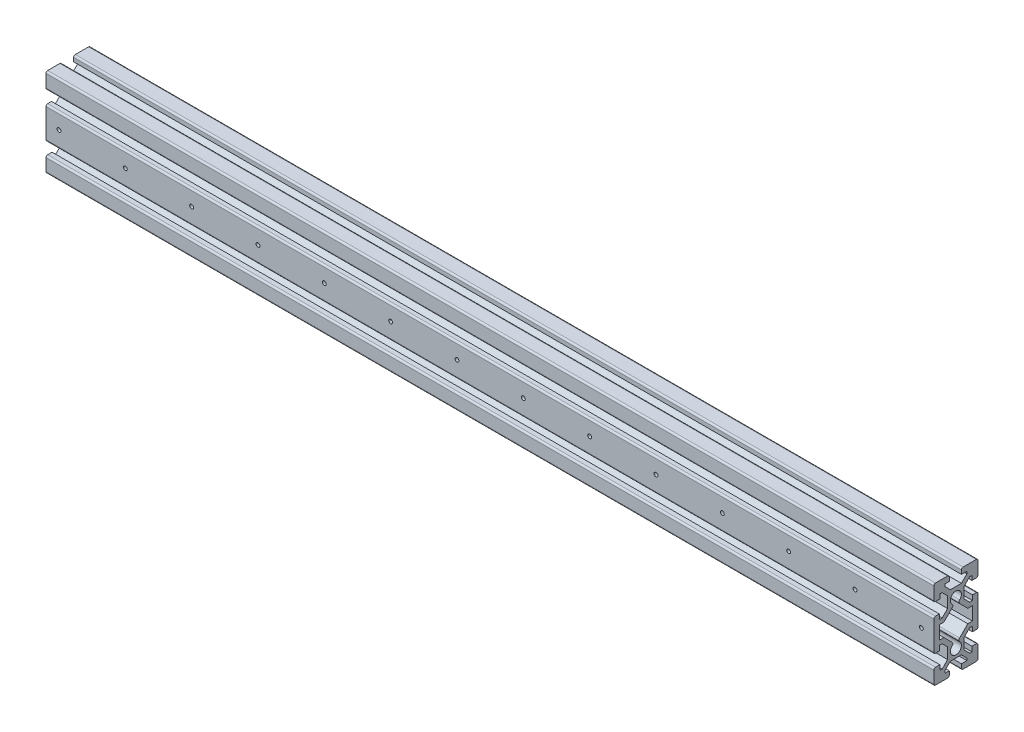
SolidWorks part; units mm, degrees
ref_plane "Piano frontale" through (0, 0, 0) normal (0, 0, 1) x (1, 0, 0)
ref_plane "Piano superiore" through (0, 0, 0) normal (0, 1, 0) x (1, 0, 0)
ref_plane "Piano destro" through (0, 0, 0) normal (1, 0, 0) x (0, 0, -1)
sketch "Schizzo1" plane through (0, 0, 0) normal (1, 0, 0) x (0, 0, -1)
  line L0 (20, 40.5) -> (5, 40.5) construction
  line L1 (18.5, -39.5) -> (6.5, -39.5)
  line L2 (-15, 6.0503) -> (-10.7929, 6.0503)
  line L3 (18.5, 40.5) -> (6.5, 40.5)
  line L4 (-20, -38) -> (-20, -27)
  line L7 (20, -39.5) -> (5, -39.5) construction
  line L21 (-12.4497, 10.0503) -> (-7.5, 15)
  line L22 (-20, -13) -> (-20, 13)
  line L23 (-18.5, 14.5) -> (-15, 14.5)
  line L24 (-14.5, 26) -> (-14.5, 29.9497)
  line L25 (-18.5, 26) -> (-14.5, 26)
  line L26 (-15, 10.0503) -> (-15, 14.5)
  line L27 (-12.4497, 10.0503) -> (-15, 10.0503)
  line L28 (-7.5, 15) -> (-7.5, 25)
  line L29 (-12.4497, 29.9497) -> (-14.5, 29.9497)
  line L30 (-12.4497, 29.9497) -> (-7.5, 25)
  line L32 (-12.4497, -29.9497) -> (-7.5, -25)
  line L33 (-12.4497, -29.9497) -> (-14.5, -29.9497)
  line L34 (-7.5, -15) -> (-7.5, -25)
  line L35 (-12.4497, -10.0503) -> (-15, -10.0503)
  line L36 (-15, -10.0503) -> (-15, -14.5)
  line L37 (-18.5, -25.5) -> (-14.5, -25.5)
  line L38 (-14.5, -25.5) -> (-14.5, -29.9497)
  line L39 (-18.5, -14.5) -> (-15, -14.5)
  line L40 (-9.9497, 35.5) -> (-6, 35.5)
  line L41 (-12.4497, -10.0503) -> (-7.5, -15)
  line L42 (20, -39.5) -> (5, -39.5) construction
  line L43 (-20, 27.5) -> (-20, 39)
  line L44 (-6, 39) -> (-6, 35.5)
  line L45 (5, 39) -> (5, 35.5)
  line L46 (9.9497, 33.4497) -> (5, 28.5)
  line L47 (-5, 28.5) -> (5, 28.5)
  line L48 (5, 35.5) -> (9.9497, 35.5)
  line L49 (-9.9497, 33.4497) -> (-9.9497, 35.5)
  line L50 (-9.9497, 33.4497) -> (-5, 28.5)
  line L51 (9.9497, 33.4497) -> (9.9497, 35.5)
  line L52 (9.9497, -32.4497) -> (9.9497, -34.5)
  line L53 (5, 40.5) -> (0, 40.5) construction
  line L54 (9.9497, 33.4497) -> (9.9497, 35.5)
  line L55 (0, -39.5) -> (5, -39.5) construction
  line L56 (9.9497, -32.4497) -> (9.9497, -34.5)
  line L57 (-9.9497, -32.4497) -> (-5, -27.5)
  line L58 (-9.9497, -32.4497) -> (-9.9497, -34.5)
  line L59 (5, -34.5) -> (9.9497, -34.5)
  line L60 (-5, -27.5) -> (5, -27.5)
  line L61 (9.9497, -32.4497) -> (5, -27.5)
  line L62 (5, -38) -> (5, -34.5)
  line L63 (-6, -38) -> (-6, -34.5)
  line L64 (-9.9497, -34.5) -> (-6, -34.5)
  line L65 (-7.5, 40.5) -> (-18.5, 40.5)
  line L66 (-7.5, -39.5) -> (-18.5, -39.5)
  line L70 (20, 27.5) -> (20, 39)
  line L71 (12.4497, -10.0503) -> (7.5, -15)
  line L72 (18.5, -14.5) -> (15, -14.5)
  line L73 (14.5, -25.5) -> (14.5, -29.9497)
  line L74 (18.5, -25.5) -> (14.5, -25.5)
  line L75 (15, -10.0503) -> (15, -14.5)
  line L76 (12.4497, -10.0503) -> (15, -10.0503)
  line L77 (7.5, -15) -> (7.5, -25)
  line L78 (12.4497, -29.9497) -> (14.5, -29.9497)
  line L79 (12.4497, -29.9497) -> (7.5, -25)
  line L80 (12.4497, 29.9497) -> (7.5, 25)
  line L81 (12.4497, 29.9497) -> (14.5, 29.9497)
  line L82 (7.5, 15) -> (7.5, 25)
  line L83 (12.4497, 10.0503) -> (15, 10.0503)
  line L84 (15, 10.0503) -> (15, 14.5)
  line L85 (18.5, 26) -> (14.5, 26)
  line L86 (14.5, 26) -> (14.5, 29.9497)
  line L87 (18.5, 14.5) -> (15, 14.5)
  line L88 (20, -13) -> (20, 13)
  line L89 (12.4497, 10.0503) -> (7.5, 15)
  line L90 (20, -38) -> (20, -27)
  line L91 (-15, 6.0503) -> (-15, -6.0503)
  line L92 (-15, 10.0503) -> (-15, 10)
  line L93 (-15, -10) -> (-15, -10.0503)
  line L94 (15, 10.0503) -> (15, 10)
  line L95 (-15, -6.0503) -> (-10.7929, -6.0503)
  line L96 (15, -10) -> (15, -10.0503)
  line L97 (15, 6.0503) -> (15, -6.0503)
  line L98 (-10.7929, 6.0503) -> (-3.3686, 13.4746)
  line L99 (10.7929, 6.0503) -> (3.3686, 13.4746)
  line L100 (10.7929, -6.0503) -> (3.3686, -13.4746)
  line L101 (-10.7929, -6.0503) -> (-3.3686, -13.4746)
  line L106 (10.7929, -6.0503) -> (15, -6.0503)
  line L107 (10.7929, 6.0503) -> (15, 6.0503)
  arc A0 (3.4163, 16.3491) -> (-3.4163, 16.3491) centre (0, 20) ccw
  arc A1 (-3.4163, -16.3491) -> (3.4163, -16.3491) centre (0, -20) ccw
  arc A2 (-3.3686, -13.4746) -> (-3.4163, -16.3491) centre (-4.7828, -14.8888) cw
  arc A3 (3.4163, -16.3491) -> (3.3686, -13.4746) centre (4.7828, -14.8888) cw
  arc A4 (3.4163, 16.3491) -> (3.3686, 13.4746) centre (4.7828, 14.8888) ccw
  arc A5 (-3.4163, 16.3491) -> (-3.3686, 13.4746) centre (-4.7828, 14.8888) cw
  arc A6 (-18.5, -25.5) -> (-20, -27) centre (-18.5, -27) ccw
  arc A7 (-7.5, -39.5) -> (-6, -38) centre (-7.5, -38) ccw
  arc A8 (6.5, -39.5) -> (5, -38) centre (6.5, -38) cw
  arc A9 (18.5, -25.5) -> (20, -27) centre (18.5, -27) cw
  arc A10 (20, -38) -> (18.5, -39.5) centre (18.5, -38) cw
  arc A11 (-18.5, -39.5) -> (-20, -38) centre (-18.5, -38) cw
  arc A12 (-20, 39) -> (-18.5, 40.5) centre (-18.5, 39) cw
  arc A13 (6.5, 40.5) -> (5, 39) centre (6.5, 39) ccw
  arc A14 (18.5, 40.5) -> (20, 39) centre (18.5, 39) cw
  arc A15 (20, 27.5) -> (18.5, 26) centre (18.5, 27.5) cw
  arc A16 (18.5, 14.5) -> (20, 13) centre (18.5, 13) cw
  arc A17 (20, -13) -> (18.5, -14.5) centre (18.5, -13) cw
  arc A18 (-18.5, -14.5) -> (-20, -13) centre (-18.5, -13) cw
  arc A19 (-20, 13) -> (-18.5, 14.5) centre (-18.5, 13) cw
  arc A20 (-18.5, 26) -> (-20, 27.5) centre (-18.5, 27.5) cw
  arc A21 (-7.5, 40.5) -> (-6, 39) centre (-7.5, 39) cw
  point P0 (0, 0)
  point P130 (-20, -25.5)
  point P166 (-20, -14.5)
  point P169 (-20, 14.5)
  point P172 (-20, 26)
  point P175 (-6, 40.5)
  dimension "D1" = 5
  dimension "D2" = 1.5
  dimension "D7" = 10
  dimension "D8" = 13.4746
  dimension "D3" = 20
  dimension "D4" = 6
  dimension "D5" = 9.9497
  dimension "D6" = 6.0503
  dimension "D9" = 25
  dimension "D10" = 14.5
  dimension "D11" = 15
  dimension "D12" = 14.5
  dimension "D13" = 25
  dimension "D14" = 29.9497
  dimension "D15" = 2
  dimension "D16" = 16.3491
  dimension "D18" = 26
  dimension "D20" = 14.5
  dimension "D21" = 15
  dimension "D22" = 20
  dimension "D25" = 35.5
  dimension "D28" = 10
  dimension "D37" = 25.5
  dimension "D42" = 39.5
extrude "Estrusione-Estrusione1" add sketch "Schizzo1" along normal blind 803
sketch "Schizzo2" plane through (0, 0, 20) normal (0, 0, 1) x (1, 0, 0)
  line L0 (803, 0.5) -> (0, 0.5) construction
  line L3 (803, -13) -> (803, 13) construction
  line L8 (803, 40.5) -> (0, 40.5) construction
  line L9 (803, 13) -> (0, 13) construction
  circle A0 centre (791.75, 0.5) radius 1.75
  circle A1 centre (731.75, 0.5) radius 1.75
  circle A2 centre (671.75, 0.5) radius 1.75
  circle A3 centre (611.75, 0.5) radius 1.75
  circle A4 centre (551.75, 0.5) radius 1.75
  circle A5 centre (491.75, 0.5) radius 1.75
  circle A6 centre (431.75, 0.5) radius 1.75
  circle A7 centre (371.75, 0.5) radius 1.75
  circle A8 centre (311.75, 0.5) radius 1.75
  circle A9 centre (251.75, 0.5) radius 1.75
  circle A10 centre (191.75, 0.5) radius 1.75
  circle A11 centre (131.75, 0.5) radius 1.75
  circle A12 centre (71.75, 0.5) radius 1.75
  circle A13 centre (11.75, 0.5) radius 1.75
  dimension "D2" = 3.5
  dimension "D1" = 11.25
  dimension "D4" = 40
  dimension "D3" = 14
extrude "Taglio-Estrusione1" cut sketch "Schizzo2" against normal blind 10
